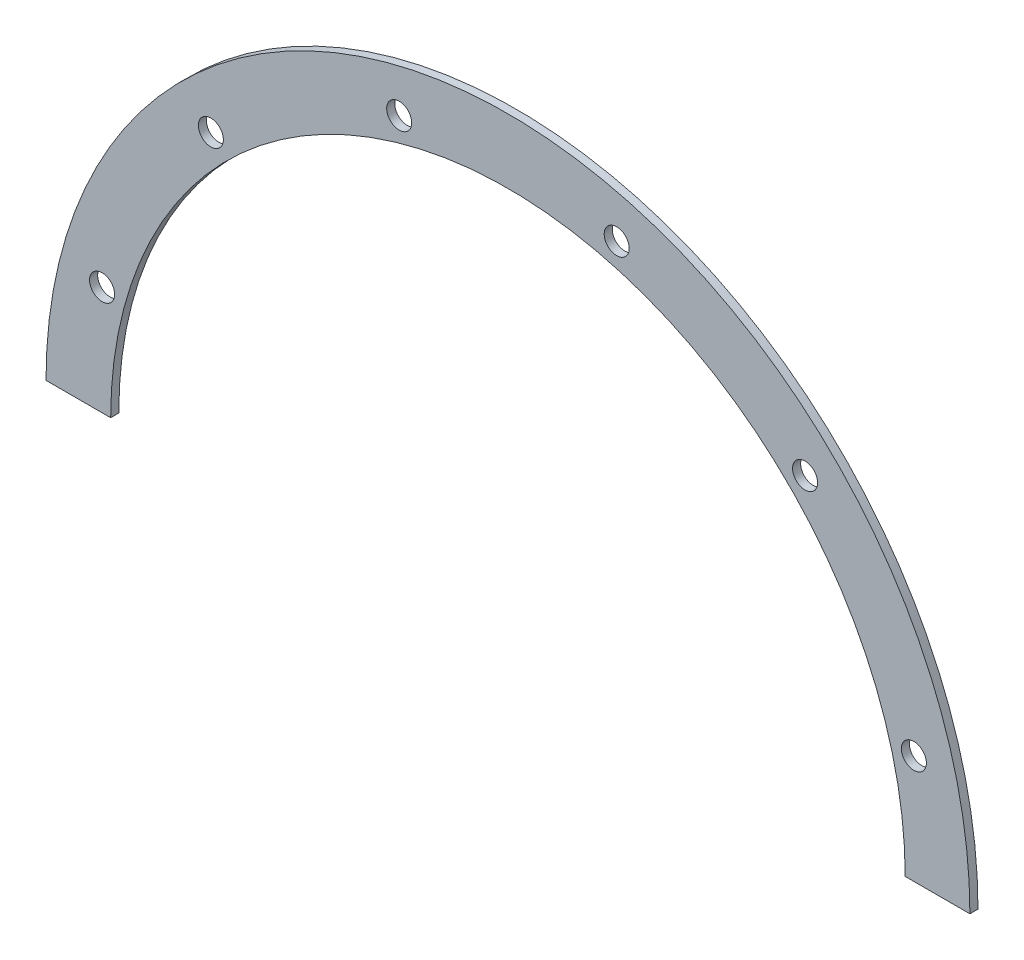
SolidWorks part; units mm, degrees
material "NEOPRENE"
ref_plane "Front Plane" through (0, 0, 0) normal (0, 0, 1) x (1, 0, 0)
ref_plane "Top Plane" through (0, 0, 0) normal (0, 1, 0) x (1, 0, 0)
ref_plane "Right Plane" through (0, 0, 0) normal (1, 0, 0) x (0, 0, -1)
sketch "Sketch1" plane through (0, 0, 0) normal (0, 0, 1) x (1, 0, 0)
  line L0 (-90.7, 0) -> (-78, 0)
  line L1 (78, 0) -> (90.7, 0)
  arc A0 (90.7, 0) -> (-90.7, 0) centre (0, 0) ccw
  arc A1 (-78, 0) -> (78, 0) centre (0, 0) cw
  dimension "D2" = 78
  dimension "D1" = 12.7
extrude "Boss-Extrude1" add sketch "Sketch1" along normal blind 1.5875
hole_wizard "#8 Clearance Hole1" positions "Sketch3" profile "Sketch2" hole size "#8" standard "ANSI Inch" end condition through all
sketch "Sketch3" plane through (0, 0, 1.5875) normal (0, 0, 1) x (1, 0, 0)
  line L0 (0, 0) -> (79.6889, 21.3526) construction
  line L2 (78, 0) -> (90.7, 0) construction
  point P0 (79.6889, 21.3526)
  dimension "D1" = 82.5
  dimension "D2" = 15
sketch "Sketch2" plane through (79.6889, 21.3526, 1.5875) normal (1, 0, 0) x (0, -1, 0)
  line L0 (0, 0) -> (0, 1.5875)
  line L1 (0, 1.5875) -> (2.4574, 1.5875)
  line L2 (2.4574, 1.5875) -> (2.4574, 0)
  line L5 (2.4574, 0) -> (0, 0)
  line L11 (0, -6.35) -> (0, 107.95) construction
  dimension "Thru Hole Dia." = 4.9149
  dimension "Thru Hole Depth" = 1.5875
pattern_circular "CirPattern1" count 6 every 30 about axis through (0, 0, 0) along (0, 0, 1) of "#8 Clearance Hole1"
